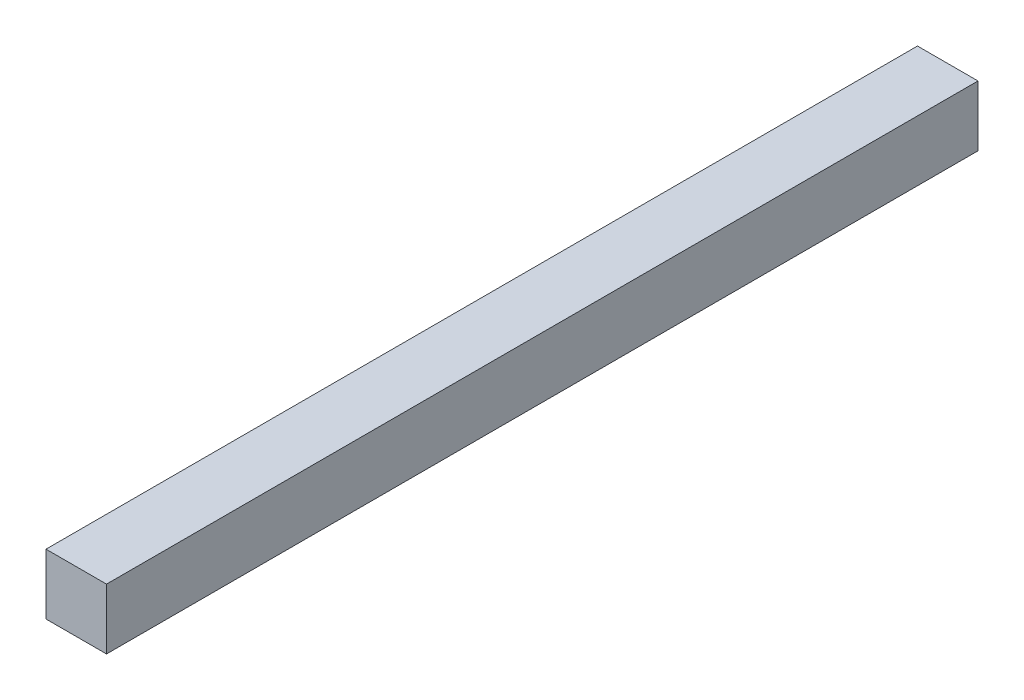
SolidWorks part; units mm, degrees
ref_plane "Front Plane" through (0, 0, 0) normal (0, 0, 1) x (1, 0, 0)
ref_plane "Top Plane" through (0, 0, 0) normal (0, 1, 0) x (1, 0, 0)
ref_plane "Right Plane" through (0, 0, 0) normal (1, 0, 0) x (0, 0, -1)
sketch "Sketch2" plane through (0, 0, 0) normal (0, 0, 1) x (1, 0, 0)
  line L1 (27.6704, 7.506) -> (34.0204, 7.506)
  line L2 (27.6704, 7.506) -> (27.6704, 13.856)
  line L3 (27.6704, 13.856) -> (34.0204, 13.856)
  line L4 (34.0204, 7.506) -> (34.0204, 13.856)
extrude "Boss-Extrude1" add sketch "Sketch2" along normal blind 91.44
